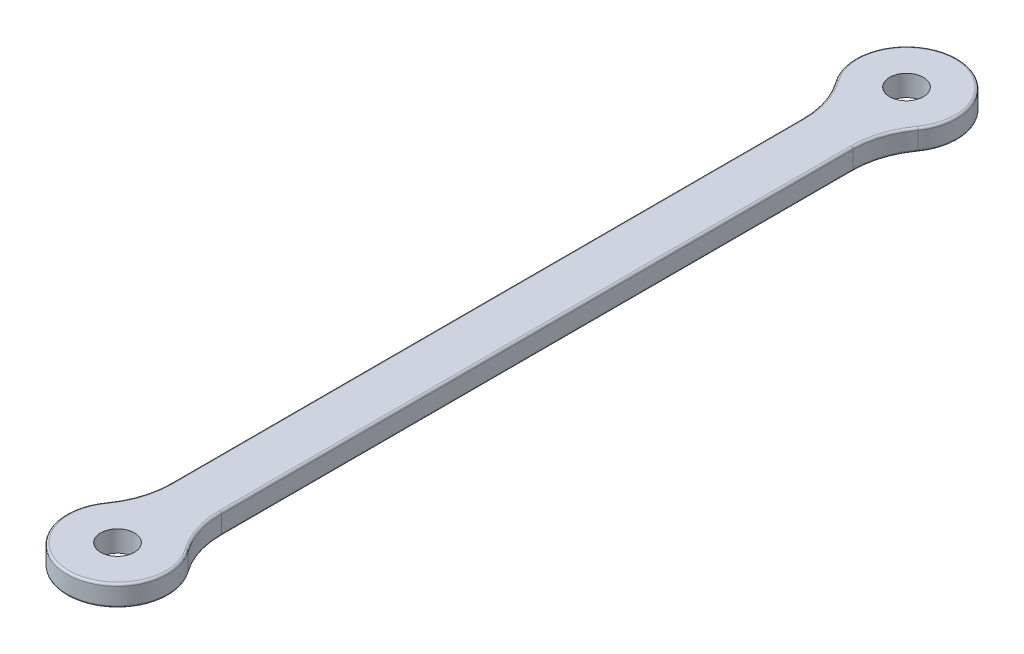
SolidWorks part; units mm, degrees
ref_plane "Front Plane" through (0, 0, 0) normal (0, 0, 1) x (1, 0, 0)
ref_plane "Top Plane" through (0, 0, 0) normal (0, 1, 0) x (1, 0, 0)
ref_plane "Right Plane" through (0, 0, 0) normal (1, 0, 0) x (0, 0, -1)
sketch "Sketch1" plane through (0, 0, 0) normal (0, 1, 0) x (1, 0, 0)
  line L1 (-3, -46.75) -> (3, -46.75)
  line L2 (-3, -46.75) -> (-3, 46.75)
  line L3 (-3, 46.75) -> (3, 46.75)
  line L4 (3, -46.75) -> (3, 46.75)
  line L5 (0, 46.75) -> (0, -46.75) construction
  line L6 (-3, 0) -> (3, 0) construction
  circle A0 centre (0, 46.75) radius 6
  circle A1 centre (0, 46.75) radius 2
  circle A2 centre (0, -46.75) radius 2
  circle A3 centre (0, -46.75) radius 6
  point P0 (0, 0)
  dimension "D2" = 12
  dimension "D5" = 4
  dimension "D3" = 93.5
  dimension "D4" = 6
extrude "Boss-Extrude1" add sketch "Sketch1" along normal blind 2.5 contours A3 L4 A0 L2 | A1 L4 A0 L2 | L2 A3 L4 A2 | L4 A3 L2 A2 | A1 L2 A0 L4
fillet "Fillet1" radius 10 4 edges at (-3, 1.25, 41.5538) (-3, 1.25, -41.5538) (3, 1.25, -41.5538) (3, 1.25, 41.5538)
fillet "Fillet2" radius 0.25 16 edges at (3.4803, 2.5, 40.4845) (3.4803, 0, 40.4845) (0, 2.5, 52.75) (0, 0, 52.75) (-3.4803, 2.5, 40.4845) (-3.4803, 0, 40.4845) (-3, 0, 0) (-3, 2.5, 0) (-3.4803, 2.5, -40.4845) (-3.4803, 0, -40.4845) (0, 0, -52.75) (0, 2.5, -52.75) (3.4803, 2.5, -40.4845) (3.4803, 0, -40.4845) (3, 0, 0) (3, 2.5, 0)
